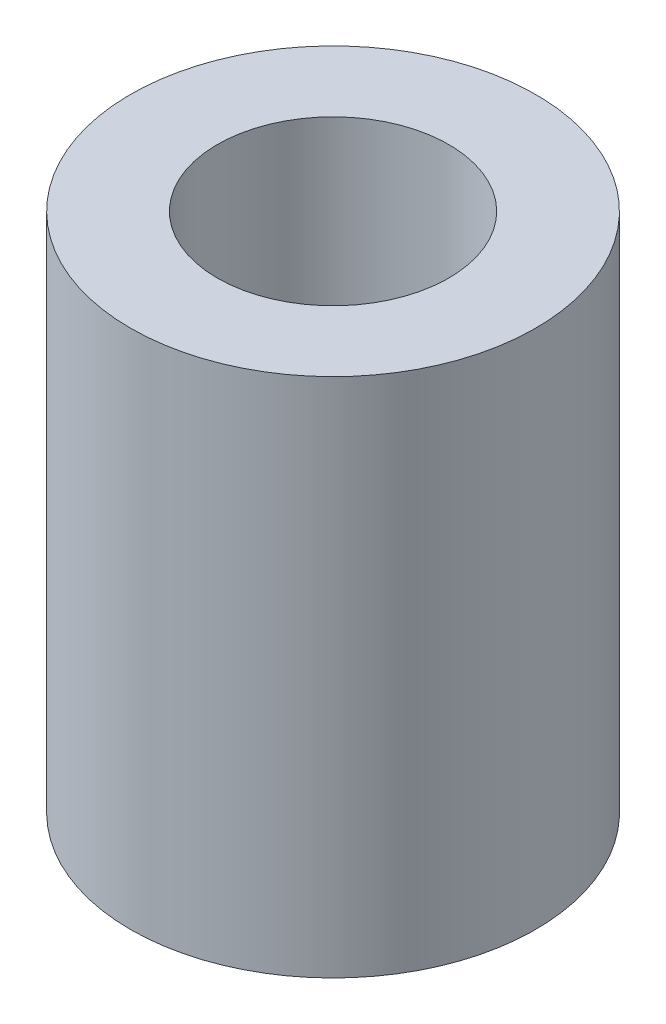
SolidWorks part; units mm, degrees
ref_plane "Front Plane" through (0, 0, 0) normal (0, 0, 1) x (1, 0, 0)
ref_plane "Top Plane" through (0, 0, 0) normal (0, 1, 0) x (1, 0, 0)
ref_plane "Right Plane" through (0, 0, 0) normal (1, 0, 0) x (0, 0, -1)
sketch "Sketch1" plane through (0, 0, 0) normal (0, 1, 0) x (1, 0, 0)
  circle A0 centre (0, 0) radius 17.5
  circle A1 centre (0, 0) radius 10
  dimension "D1" = 35
  dimension "D2" = 20
extrude "Boss-Extrude1" add sketch "Sketch1" along normal blind 45
